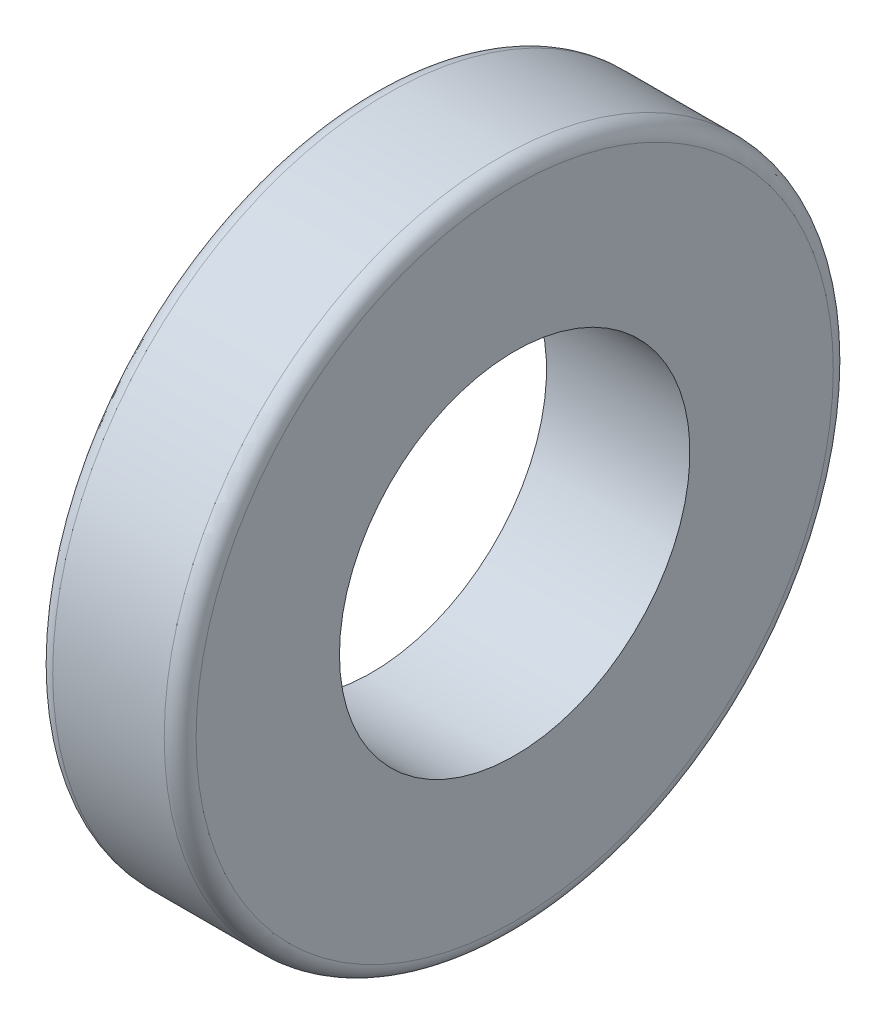
SolidWorks part; units mm, degrees
ref_plane "Front Plane" through (0, 0, 0) normal (0, 0, 1) x (1, 0, 0)
ref_plane "Top Plane" through (0, 0, 0) normal (0, 1, 0) x (1, 0, 0)
ref_plane "Right Plane" through (0, 0, 0) normal (1, 0, 0) x (0, 0, -1)
sketch "Sketch1" plane through (0, 0, 0) normal (0, 0, 1) x (1, 0, 0)
  line L0 (0, 0) -> (6, 0) construction
  line L2 (0.75, 10.5) -> (5.25, 10.5)
  line L3 (0.75, 10.5) -> (0.75, 5.5)
  line L4 (0.75, 5.5) -> (5.25, 5.5)
  line L5 (5.25, 10.5) -> (5.25, 5.5)
  line L6 (0.75, 10.5) -> (5.25, 5.5) construction
  line L7 (0.75, 5.5) -> (5.25, 10.5) construction
  point P3 (3, 8)
  point P9 (0, 0)
  point P10 (3, 0)
  dimension "D1" = 10.5
  dimension "D2" = 4.5
  dimension "D3" = 5
  dimension "D4" = 6
revolve "Revolve1" add sketch "Sketch1" angle 360 about L0
fillet "Fillet1" radius 0.5 2 edges at (0.75, 0, 10.5) (5.25, 0, 10.5)
